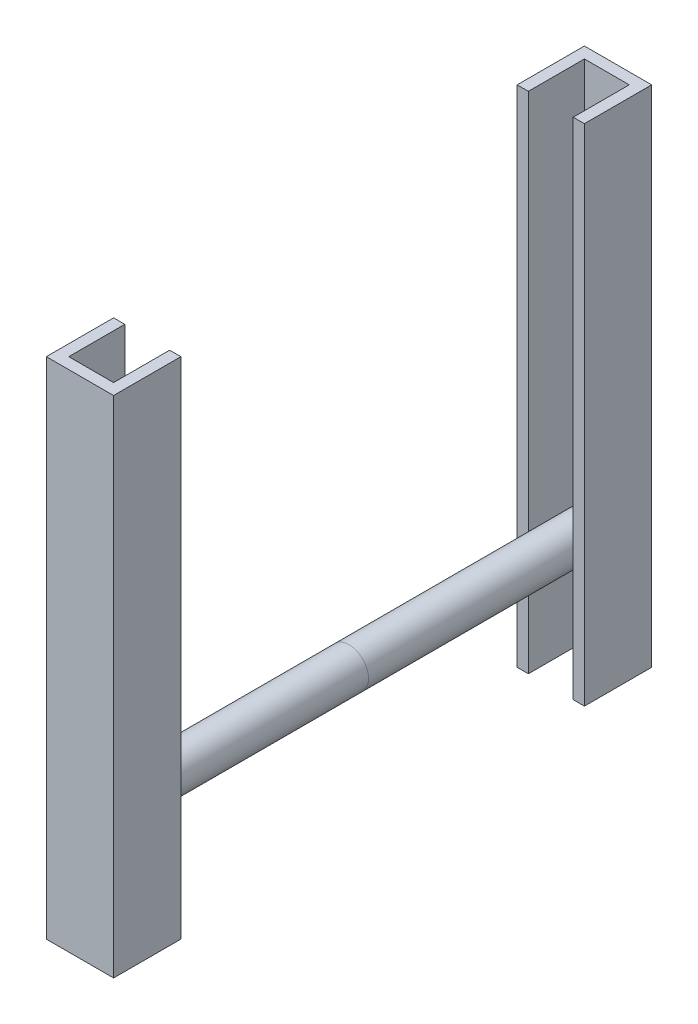
SolidWorks part; units mm, degrees
ref_plane "Front Plane" through (0, 0, 0) normal (0, 0, 1) x (1, 0, 0)
ref_plane "Top Plane" through (0, 0, 0) normal (0, 1, 0) x (1, 0, 0)
ref_plane "Right Plane" through (0, 0, 0) normal (1, 0, 0) x (0, 0, -1)
sketch "Sketch2" plane through (0, 0, 0) normal (0, 1, 0) x (1, 0, 0)
  line L0 (-20, 20) -> (-20, 30)
  line L1 (-30, -30) -> (30, -30)
  line L2 (-30, -30) -> (-30, 30)
  line L3 (-30, 30) -> (-20, 30)
  line L4 (30, -30) -> (30, 30)
  line L5 (-30, -30) -> (30, 30) construction
  line L6 (-30, 30) -> (30, -30) construction
  line L7 (-20, -20) -> (20, -20)
  line L8 (-20, -20) -> (-20, 20)
  line L10 (20, -20) -> (20, 20)
  line L11 (-20, -20) -> (20, 20) construction
  line L12 (-20, 20) -> (20, -20) construction
  line L13 (20, 20) -> (20, 30)
  line L14 (20, 30) -> (30, 30)
  point P0 (0, 0)
  point P6 (0, 0)
  dimension "60" = 60
  dimension "D2" = 40
extrude "Boss-Extrude1" add sketch "Sketch2" along normal mid plane 450
sketch "Sketch3" plane through (0, 0, 0) normal (0, 0, 1) x (1, 0, 0)
  line L0 (0, 225) -> (0, -225) construction
  line L1 (-30, 225) -> (30, 225) construction
  line L2 (-30, -225) -> (30, -225) construction
  circle A0 centre (0, -120) radius 17.5
  point P6 (0, -120)
  dimension "D2" = 35
  dimension "D1" = 105
extrude "Boss-Extrude2" add sketch "Sketch3" against normal blind 210 separate body
mirror "Mirror3" about plane through (0, -120, -210) normal (0, 0, 1) of bodies 102 101
